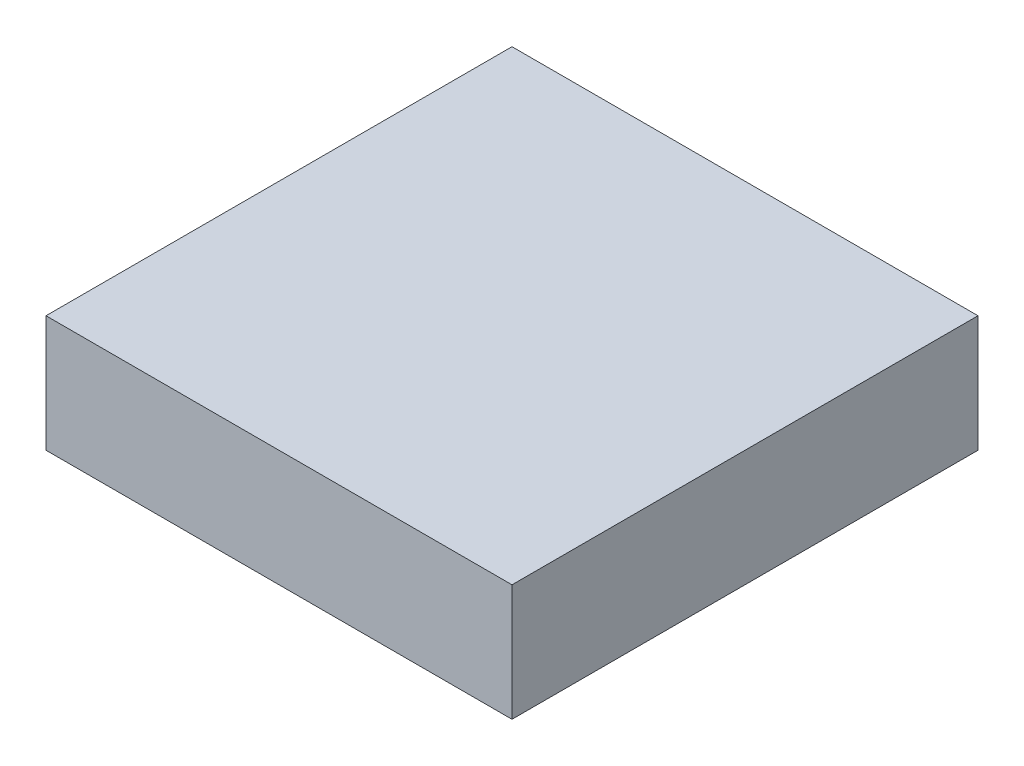
SolidWorks part; units mm, degrees
ref_plane "Front Plane" through (0, 0, 0) normal (0, 0, 1) x (1, 0, 0)
ref_plane "Top Plane" through (0, 0, 0) normal (0, 1, 0) x (1, 0, 0)
ref_plane "Right Plane" through (0, 0, 0) normal (1, 0, 0) x (0, 0, -1)
sketch "Sketch1" plane through (0, 0, 0) normal (0, 1, 0) x (1, 0, 0)
  line L1 (-3.0409, 1.8298) -> (0.9591, 1.8298)
  line L2 (-3.0409, 1.8298) -> (-3.0409, -2.1702)
  line L3 (-3.0409, -2.1702) -> (0.9591, -2.1702)
  line L4 (0.9591, 1.8298) -> (0.9591, -2.1702)
  dimension "D1" = 4
  dimension "D2" = 4
extrude "Boss-Extrude1" add sketch "Sketch1" along normal blind 1
